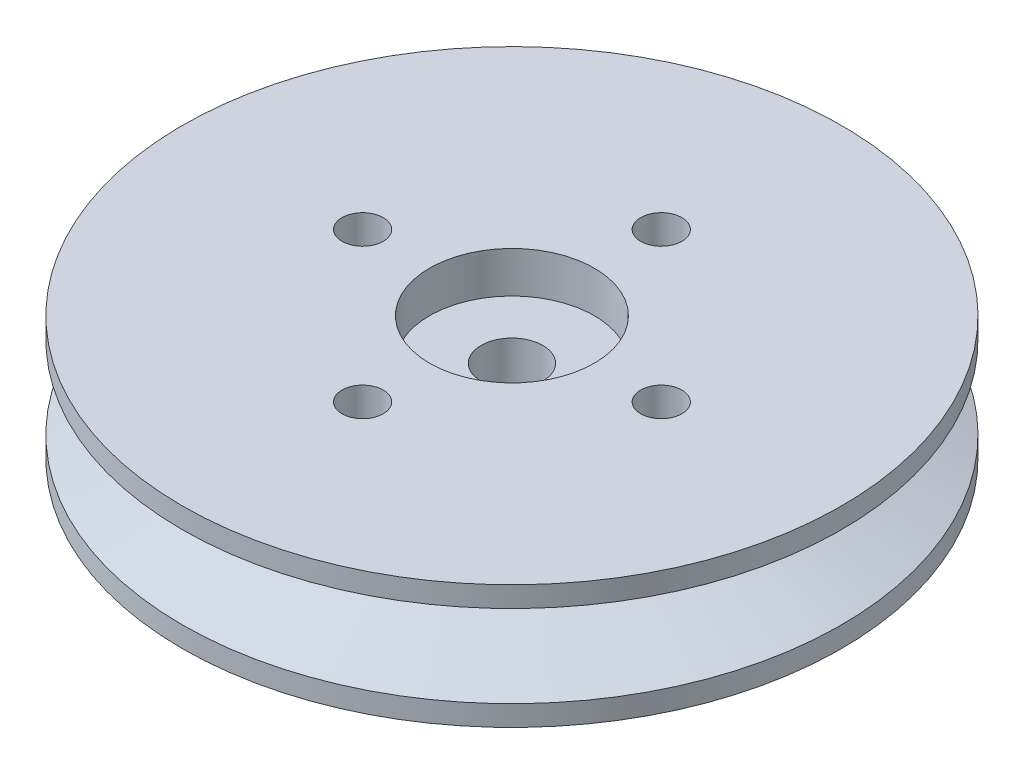
SolidWorks part; units mm, degrees
ref_plane "Front Plane" through (0, 0, 0) normal (0, 0, 1) x (1, 0, 0)
ref_plane "Top Plane" through (0, 0, 0) normal (0, 1, 0) x (1, 0, 0)
ref_plane "Right Plane" through (0, 0, 0) normal (1, 0, 0) x (0, 0, -1)
sketch "Sketch1" plane through (0, 0, 0) normal (0, 1, 0) x (1, 0, 0)
  line L0 (0, 0) -> (0, 7.25) construction
  circle A0 centre (0, 0) radius 16
  circle A2 centre (0, 7.25) radius 1
  circle A3 centre (7.25, 0) radius 1
  circle A4 centre (0, -7.25) radius 1
  circle A5 centre (-7.25, 0) radius 1
  circle A6 centre (0, 0) radius 1.5
  point P15 (0, 0)
  dimension "D1" = 32
  dimension "D2" = 3
  dimension "D4" = 2
  dimension "D3" = 7.25
  dimension "D5" = 4
extrude "Boss-Extrude1" add sketch "Sketch1" along normal blind 6
sketch "Sketch2" plane through (0, 6, 0) normal (0, 1, 0) x (1, 0, 0)
  circle A0 centre (0, 0) radius 4
  dimension "D1" = 8
extrude "Cut-Extrude1" cut sketch "Sketch2" against normal blind 2
sketch "Sketch3" plane through (0, 0, 0) normal (1, 0, 0) x (0, 0, -1)
  line L0 (-16, 6) -> (-16, 5) construction
  line L1 (-16, 5) -> (-12, 5) construction
  line L2 (-12, 5) -> (-12, 3.5) construction
  line L3 (-16, 5) -> (-12, 3.5)
  line L4 (-12, 1) -> (-12, 2.5) construction
  line L5 (-16, 0) -> (-16, 1) construction
  line L7 (-16, 1) -> (-12, 1) construction
  line L8 (-12, 2.5) -> (-16, 1)
  line L9 (-16, 1) -> (-16, 5)
  line L10 (-12, 3.5) -> (-12, 2.5)
  dimension "D1" = 1
  dimension "D2" = 4
  dimension "D3" = 1.5
  dimension "D4" = 1.5
  dimension "D5" = 1
  dimension "D6" = 4
revolve "Cut-Revolve1" cut sketch "Sketch3" angle 360 about axis through (0, 6, 0) along (0, -1, 0)
